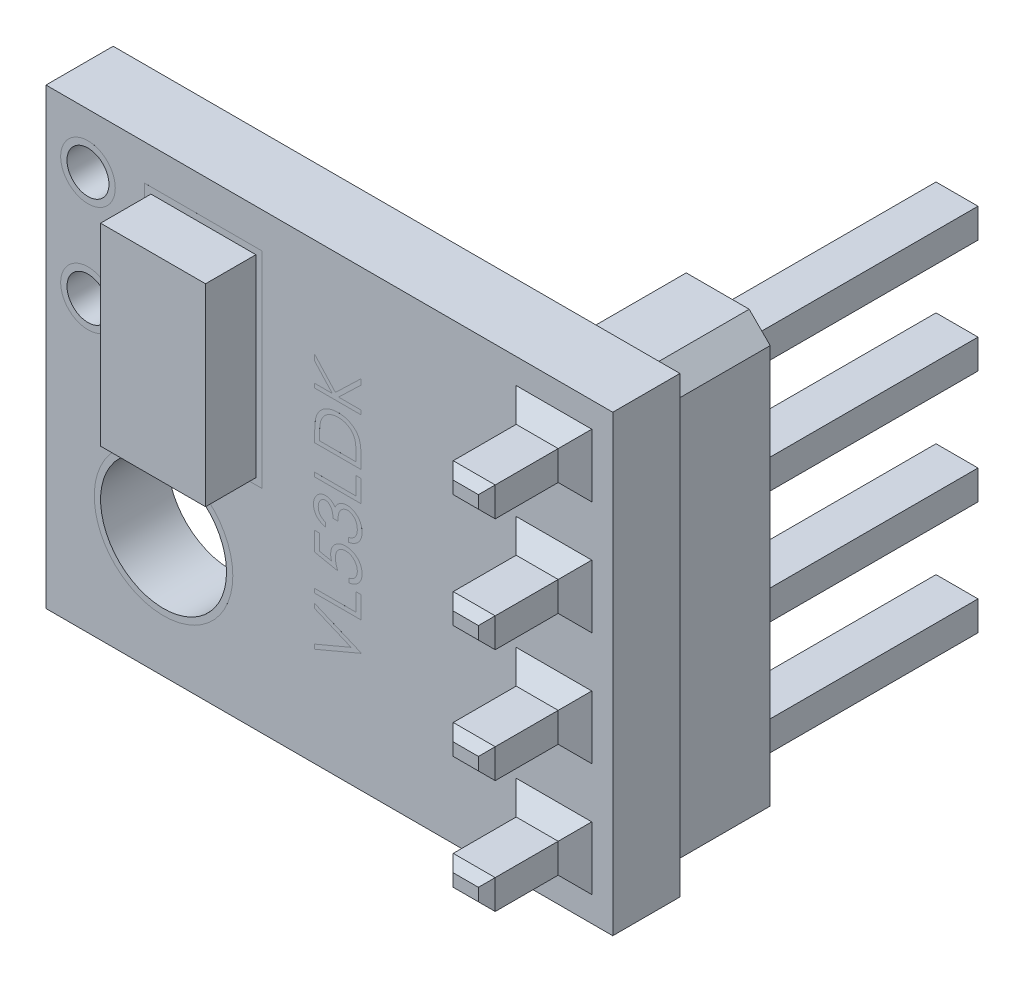
SolidWorks part; units mm, degrees
material "Placa de circuito de energia"
ref_plane "Plano frontal" through (0, 0, 0) normal (0, 0, 1) x (1, 0, 0)
ref_plane "Plano superior" through (0, 0, 0) normal (0, 1, 0) x (1, 0, 0)
ref_plane "Plano direito" through (0, 0, 0) normal (1, 0, 0) x (0, 0, -1)
sketch "Sketch1" plane through (0, 0, 0) normal (0, 0, 1) x (1, 0, 0)
  line L1 (-6.75, 5.4) -> (6.75, 5.4)
  line L2 (-6.75, 5.4) -> (-6.75, -5.4)
  line L3 (-6.75, -5.4) -> (6.75, -5.4)
  line L4 (6.75, 5.4) -> (6.75, -5.4)
  point P4 (0, 5.4)
  point P6 (-6.75, 0)
  dimension "D1" = 13.5
  dimension "D2" = 10.8
extrude "Boss-Extrude1" add sketch "Sketch1" along normal mid plane 1.6
sketch "Sketch2" plane through (0, 0, 0.8) normal (0, 0, 1) x (1, 0, 0)
  line L1 (-4.25, 4.4) -> (-1.75, 4.4)
  line L2 (-4.25, 4.4) -> (-4.25, -0.2)
  line L3 (-4.25, -0.2) -> (-1.75, -0.2)
  line L4 (-1.75, 4.4) -> (-1.75, -0.2)
  line L5 (0, -5.4) -> (0, 5.4) construction
  line L6 (-6.75, 5.4) -> (-6.75, -5.4) construction
  line L7 (-6.75, -5.4) -> (6.75, -5.4) construction
  line L8 (6.75, 5.4) -> (-6.75, 5.4) construction
  point P8 (0, 0)
  dimension "D1" = 2.5
  dimension "D2" = 4.6
  dimension "D3" = 5.2
  dimension "D4" = 2.5
  dimension "D5" = 1.75
extrude "Boss-Extrude2" add sketch "Sketch2" along normal blind 1.2
sketch "Sketch3" plane through (0, 0, 0) normal (0, 0, 1) x (1, 0, 0)
  line L1 (-6.75, -5.4) -> (6.75, -5.4) construction
  line L3 (-6.75, 5.4) -> (-6.75, -5.4) construction
  circle A0 centre (-3.95, -2.5) radius 1.5
  dimension "D1" = 3
  dimension "D2" = 1.4
  dimension "D3" = 1.3
extrude "Cut-Extrude1" cut sketch "Sketch3" against normal through all both and the other way through all
sketch "Sketch6" plane through (0, 0, 0) normal (0, 0, 1) x (1, 0, 0)
  line L2 (-6.75, 5.4) -> (-6.75, -5.4) construction
  line L5 (-4.25, 4.4) -> (-4.25, -0.2) construction
  line L10 (-1.75, 4.4) -> (-4.25, 4.4) construction
  circle A0 centre (-5.75, 4.1) radius 0.5
  circle A1 centre (-5.75, 1.5) radius 0.5
  dimension "D1" = 1
  dimension "D2" = 0.5
  dimension "D3" = 1
  dimension "D4" = 1.6
  dimension "D5" = 0.2
extrude "Cut-Extrude2" cut sketch "Sketch6" against normal through all both and the other way through all
sketch "Sketch7" plane through (0, 0, 0.8) normal (0, 0, 1) x (1, 0, 0)
  circle A11 centre (-5.75, 1.5) radius 0.65
  circle A12 centre (-5.75, 1.5) radius 0.65
  circle A14 centre (-5.75, 4.1) radius 0.65
  circle A15 centre (-5.75, 4.1) radius 0.65
  circle A16 centre (-3.95, -2.5) radius 1.5 construction
  circle A17 centre (-3.95, -2.5) radius 1.65
  circle A18 centre (-3.95, -2.5) radius 1.65
  circle A19 centre (-5.75, 4.1) radius 0.5 construction
  circle A20 centre (-5.75, 1.5) radius 0.5 construction
  circle A21 centre (-3.95, -2.5) radius 1.5
  circle A22 centre (-5.75, 4.1) radius 0.5
  circle A23 centre (-5.75, 1.5) radius 0.5
  dimension "D1" = 0.15
  dimension "D2" = 0.15
  dimension "D3" = 0.15
extrude "Boss-Extrude6" add sketch "Sketch7" along normal blind 0.0001
sketch "Sketch8" plane through (0, 0, 0.8) normal (0, 0, 1) x (1, 0, 0)
  line L0 (0.75, -3.9106) -> (0.75, 3.9106) construction
  line L1 (6.75, -5.4) -> (6.75, 5.4) construction
  line L2 (-4.4, 4.55) -> (-4.4, -0.35)
  line L3 (-4.4, -0.35) -> (-1.6, -0.35)
  line L4 (-1.6, -0.35) -> (-1.6, 4.55)
  line L5 (-1.6, 4.55) -> (-4.4, 4.55)
  line L6 (-4.25, 4.4) -> (-4.25, -0.2)
  line L7 (-4.25, -0.2) -> (-1.75, -0.2)
  line L8 (-1.75, -0.2) -> (-1.75, 4.4)
  line L9 (-1.75, 4.4) -> (-4.25, 4.4)
  line L10 (-4.25, 4.4) -> (-4.25, -0.2)
  line L11 (-4.25, -0.2) -> (-1.75, -0.2)
  line L12 (-1.75, -0.2) -> (-1.75, 4.4)
  line L13 (-1.75, 4.4) -> (-4.25, 4.4)
  text T0 "VL53LDK" font "Century Gothic" height 1.1
  point P4 (0, 0)
  dimension "D1" = 6
  dimension "D2" = 0
  dimension "D3" = 0.15
extrude "Boss-Extrude7" add sketch "Sketch8" along normal blind 0.0001
mirror "Mirror1" about plane through (0, 0, 0) normal (0, 0, 1) of "Boss-Extrude6"
sketch "Sketch4" plane through (0, 0, -0.8) normal (0, 0, -1) x (-1, 0, 0)
  line L0 (-6.75, 5.4) -> (6.75, 5.4) construction
  line L1 (-4.1, 5.25) -> (-6.6, 5.25)
  line L2 (-4.1, 5.25) -> (-4.1, -5.25)
  line L3 (-4.1, -5.25) -> (-6.6, -5.25)
  line L4 (-6.6, 5.25) -> (-6.6, -5.25)
  line L7 (-6.75, -5.4) -> (-6.75, 5.4) construction
  point P4 (-4.1, 0)
  dimension "D1" = 0.15
  dimension "D2" = 2.5
  dimension "D3" = 0.15
extrude "Boss-Extrude3" add sketch "Sketch4" along normal blind 2.3
sketch "Sketch5" plane through (0, 0, -3.1) normal (0, 0, -1) x (-1, 0, 0)
  line L0 (-4.1, 5.25) -> (-6.6, 5.25) construction
  line L1 (-5.85, 4.4) -> (-4.85, 4.4) construction
  line L2 (-5.85, 4.4) -> (-5.85, -4.4) construction
  line L3 (-5.85, -4.4) -> (-4.85, -4.4) construction
  line L4 (-4.85, 4.4) -> (-4.85, -4.4) construction
  line L5 (-4.85, 1.7) -> (-5.85, 1.7)
  line L6 (-4.85, 4.4) -> (-5.85, 4.4)
  line L7 (-4.85, 4.4) -> (-4.85, 3.7)
  line L8 (-4.85, 3.7) -> (-5.85, 3.7)
  line L9 (-5.85, 4.4) -> (-5.85, 3.7)
  line L10 (-4.85, 1.7) -> (-4.85, 1)
  line L11 (-4.85, 1) -> (-5.85, 1)
  line L12 (-5.85, 1.7) -> (-5.85, 1)
  line L13 (-5.85, 1.7) -> (-4.85, 1.7) construction
  line L14 (-4.85, -1) -> (-5.85, -1)
  line L15 (-4.85, -1) -> (-4.85, -1.7)
  line L16 (-4.85, -1.7) -> (-5.85, -1.7)
  line L17 (-5.85, -1) -> (-5.85, -1.7)
  line L18 (-5.85, -1) -> (-4.85, -1) construction
  line L19 (-4.85, -3.7) -> (-5.85, -3.7)
  line L20 (-4.85, -3.7) -> (-4.85, -4.4)
  line L21 (-4.85, -4.4) -> (-5.85, -4.4)
  line L22 (-5.85, -3.7) -> (-5.85, -4.4)
  line L23 (-5.85, -3.7) -> (-4.85, -3.7) construction
  line L24 (-4.85, 4.4) -> (-4.85, 1.7) construction
  line L25 (-4.1, 5.25) -> (-6.6, 5.25) construction
  point P4 (-4.85, 0)
  point P9 (-5.35, 5.25)
  point P10 (-5.35, 4.4)
  dimension "D1" = 0.85
  dimension "D2" = 1
  dimension "D3" = 0.7
  dimension "D5" = 2
  dimension "D4" = 4
extrude "Boss-Extrude4" add sketch "Sketch5" along normal blind 5.9 and the other way blind 6
chamfer "Chamfer3" distance 0.2 angle 45 32 edges at (5.35, 3.7, 2.9) (4.85, 4.05, 2.9) (5.35, 4.4, 2.9) (5.85, 4.05, 2.9) (5.35, 1, 2.9) (4.85, 1.35, 2.9) (5.35, 1.7, 2.9) (5.85, 1.35, 2.9) (5.35, -1.7, 2.9) (4.85, -1.35, 2.9) (5.35, -1, 2.9) (5.85, -1.35, 2.9) (5.35, -4.4, 2.9) (4.85, -4.05, 2.9) (5.35, -3.7, 2.9) (5.85, -4.05, 2.9) (5.35, -3.7, -9) (4.85, -4.05, -9) (5.35, -4.4, -9) (5.85, -4.05, -9) (5.35, -1, -9) (4.85, -1.35, -9) (5.35, -1.7, -9) (5.85, -1.35, -9) (5.35, 1.7, -9) (4.85, 1.35, -9) (5.35, 1, -9) (5.85, 1.35, -9) (5.35, 4.4, -9) (4.85, 4.05, -9) (5.35, 3.7, -9) (5.85, 4.05, -9)
chamfer "Chamfer1" distance 0.4 angle 45 16 edges at (5.85, 1.35, 0.8) (5.35, 1.7, 0.8) (5.35, 1, 0.8) (4.85, 1.35, 0.8) (5.85, 4.05, 0.8) (5.35, 3.7, 0.8) (4.85, 4.05, 0.8) (5.35, 4.4, 0.8) (5.35, -1, 0.8) (4.85, -1.35, 0.8) (5.35, -1.7, 0.8) (5.85, -1.35, 0.8) (5.35, -3.7, 0.8) (5.85, -4.05, 0.8) (4.85, -4.05, 0.8) (5.35, -4.4, 0.8)
chamfer "Chamfer2" distance 0.5 angle 45 4 edges at (4.1, -5.25, -1.95) (6.6, -5.25, -1.95) (6.6, 5.25, -1.95) (4.1, 5.25, -1.95)
